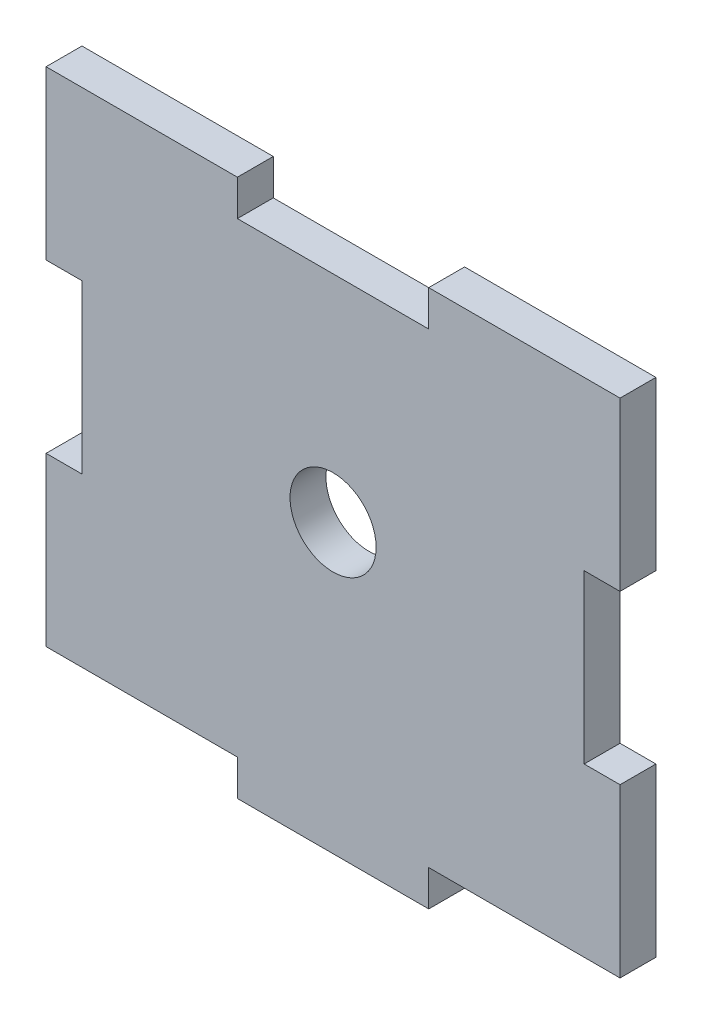
SolidWorks part; units mm, degrees
ref_plane "Alzado" through (0, 0, 0) normal (0, 0, 1) x (1, 0, 0)
ref_plane "Planta" through (0, 0, 0) normal (0, 1, 0) x (1, 0, 0)
ref_plane "Vista lateral" through (0, 0, 0) normal (1, 0, 0) x (0, 0, -1)
sketch "Croquis1" plane through (0, 0, 0) normal (0, 0, 1) x (1, 0, 0)
  line L0 (40, 75) -> (40, 48.9607) construction
  line L1 (0, 0) -> (80, 0)
  line L2 (0, 0) -> (0, 75)
  line L3 (0, 75) -> (80, 75)
  line L4 (80, 0) -> (80, 75)
  line L5 (0, 75) -> (5, 75)
  line L6 (0, 75) -> (0, 0)
  line L7 (0, 0) -> (5, 0)
  line L8 (5, 75) -> (5, 0)
  line L9 (0, 0) -> (80, 0)
  line L10 (0, 0) -> (0, 5)
  line L11 (0, 5) -> (80, 5)
  line L12 (80, 0) -> (80, 5)
  line L13 (26.6667, 5) -> (26.6667, 0)
  line L14 (53.3333, 5) -> (53.3333, 0)
  line L15 (0, 51.6667) -> (5, 51.6667)
  line L16 (0, 28.3333) -> (5, 28.3333)
  line L17 (75, 75) -> (75, 0)
  line L18 (80, 28.3333) -> (75, 28.3333)
  line L19 (80, 51.6667) -> (75, 51.6667)
  point P19 (53.3333, 2.5)
  dimension "D1" = 80
  dimension "D2" = 75
  dimension "D3" = 5
  dimension "D4" = 5
  dimension "D5" = 23.3333
  dimension "D6" = 23.3333
  dimension "D7" = 26.6667
  dimension "D8" = 26.6667
extrude "Saliente-Extruir1" add sketch "Croquis1" along normal blind 5
sketch "Croquis2" plane through (0, 0, 5) normal (0, 0, 1) x (1, 0, 0)
  line L0 (0, 75) -> (80, 75) construction
  line L1 (53.3333, 75) -> (26.6667, 75)
  line L2 (53.3333, 75) -> (53.3333, 70)
  line L3 (53.3333, 70) -> (26.6667, 70)
  line L4 (26.6667, 75) -> (26.6667, 70)
  line L6 (0, 51.6667) -> (0, 75) construction
  line L7 (80, 51.6667) -> (80, 75) construction
  dimension "D1" = 5
  dimension "D2" = 26.6667
  dimension "D3" = 26.6667
extrude "Cortar-Extruir1" cut sketch "Croquis2" against normal blind 10
sketch "Croquis5" plane through (0, 0, 5) normal (0, 0, 1) x (1, 0, 0)
  line L0 (40, 70) -> (40, 40)
  line L1 (26.6667, 70) -> (53.3333, 70) construction
  line L2 (75, 40) -> (40, 40)
  line L3 (75, 51.6667) -> (75, 28.3333) construction
  circle A0 centre (40, 40) radius 6
  dimension "D1" = 12
extrude "Cortar-Extruir3" cut sketch "Croquis5" against normal blind 10 contours L0 A0 L2 | L2 A0 L0
sketch "Croquis6" plane through (0, 0, 5) normal (0, 0, 1) x (1, 0, 0)
  line L20 (53.3333, 75) -> (53.3333, 70)
  line L21 (53.3333, 70) -> (26.6667, 70)
  line L22 (26.6667, 70) -> (26.6667, 75)
  line L23 (26.6667, 75) -> (0, 75)
  line L24 (0, 75) -> (0, 51.6667)
  line L25 (0, 51.6667) -> (5, 51.6667)
  line L26 (5, 51.6667) -> (5, 28.3333)
  line L27 (5, 28.3333) -> (0, 28.3333)
  line L28 (0, 28.3333) -> (0, 5)
  line L29 (0, 5) -> (26.6667, 5)
  line L30 (26.6667, 5) -> (26.6667, 0)
  line L31 (26.6667, 0) -> (53.3333, 0)
  line L32 (53.3333, 0) -> (53.3333, 5)
  line L33 (53.3333, 5) -> (80, 5)
  line L34 (80, 5) -> (80, 28.3333)
  line L35 (80, 28.3333) -> (75, 28.3333)
  line L36 (75, 28.3333) -> (75, 51.6667)
  line L37 (75, 51.6667) -> (80, 51.6667)
  line L38 (80, 51.6667) -> (80, 75)
  line L39 (80, 75) -> (53.3333, 75)
  line L40 (53.3333, 75) -> (53.3333, 70)
  line L41 (53.3333, 70) -> (26.6667, 70)
  line L42 (26.6667, 70) -> (26.6667, 75)
  line L43 (26.6667, 75) -> (0, 75)
  line L44 (0, 75) -> (0, 51.6667)
  line L45 (0, 51.6667) -> (5, 51.6667)
  line L46 (5, 51.6667) -> (5, 28.3333)
  line L47 (5, 28.3333) -> (0, 28.3333)
  line L48 (0, 28.3333) -> (0, 5)
  line L49 (0, 5) -> (26.6667, 5)
  line L50 (26.6667, 5) -> (26.6667, 0)
  line L51 (26.6667, 0) -> (53.3333, 0)
  line L52 (53.3333, 0) -> (53.3333, 5)
  line L53 (53.3333, 5) -> (80, 5)
  line L54 (80, 5) -> (80, 28.3333)
  line L55 (80, 28.3333) -> (75, 28.3333)
  line L56 (75, 28.3333) -> (75, 51.6667)
  line L57 (75, 51.6667) -> (80, 51.6667)
  line L58 (80, 51.6667) -> (80, 75)
  line L59 (80, 75) -> (53.3333, 75)
  circle A0 centre (40, 40) radius 6 construction
  circle A1 centre (40, 40) radius 6
  dimension "D1" = 0
